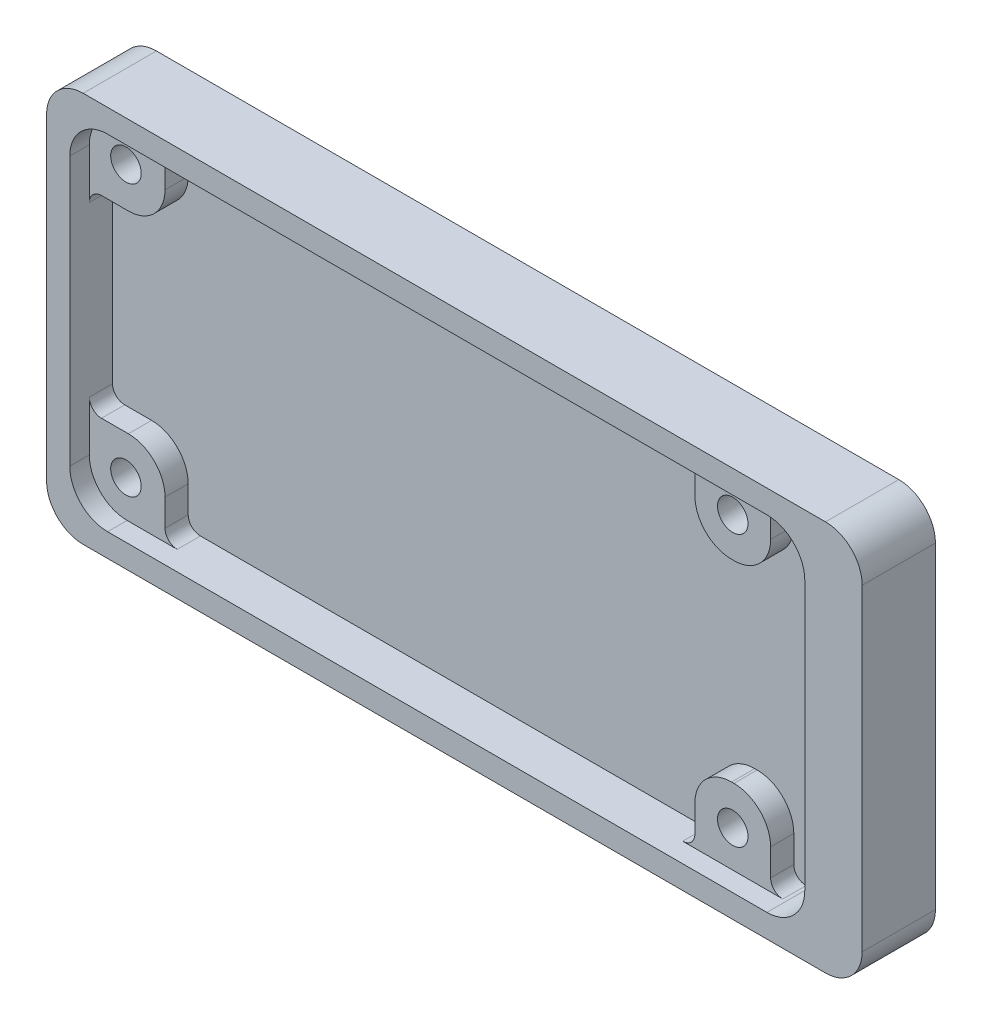
SolidWorks part; units mm, degrees
ref_plane "Спереди" through (0, 0, 0) normal (0, 0, 1) x (1, 0, 0)
ref_plane "Сверху" through (0, 0, 0) normal (0, 1, 0) x (1, 0, 0)
ref_plane "Справа" through (0, 0, 0) normal (1, 0, 0) x (0, 0, -1)
sketch "Эскиз1" plane through (0, 0, 0) normal (0, 0, 1) x (1, 0, 0)
  line L1 (3, 0) -> (63.8, 0)
  line L2 (0, 3) -> (0, 29)
  line L3 (3, 32) -> (63.8, 32)
  line L4 (66.8, 3) -> (66.8, 29)
  arc A0 (63.8, 0) -> (66.8, 3) centre (63.8, 3) ccw
  arc A1 (63.8, 32) -> (66.8, 29) centre (63.8, 29) cw
  arc A2 (3, 0) -> (0, 3) centre (3, 3) cw
  arc A3 (0, 29) -> (3, 32) centre (3, 29) cw
  point P9 (66.8, 32)
  point P12 (0, 0)
  point P15 (0, 32)
  dimension "D3" = 3
  dimension "D1" = 66.8
  dimension "D2" = 32
extrude "Бобышка-Вытянуть1" add sketch "Эскиз1" along normal blind 6
sketch "Эскиз2" plane through (0, 0, 6) normal (0, 0, 1) x (1, 0, 0)
  line L0 (0, 29) -> (0, 3) construction
  line L1 (5, 30.1) -> (59, 30.1)
  line L2 (1.9, 27) -> (1.9, 5)
  line L3 (5, 1.9) -> (59, 1.9)
  line L4 (62.1, 27) -> (62.1, 5)
  line L6 (63.8, 32) -> (3, 32) construction
  arc A0 (59, 30.1) -> (62.1, 27) centre (59, 27) cw
  arc A1 (59, 1.9) -> (62.1, 5) centre (59, 5) ccw
  arc A2 (1.9, 5) -> (5, 1.9) centre (5, 5) ccw
  arc A3 (5, 30.1) -> (1.9, 27) centre (5, 27) ccw
  point P10 (62.1, 30.1)
  point P15 (1.9, 1.9)
  point P18 (1.9, 30.1)
  dimension "D5" = 3.1
  dimension "D1" = 60.2
  dimension "D2" = 28.2
  dimension "D3" = 1.9
  dimension "D4" = 1.9
extrude "Вырез-Вытянуть1" cut sketch "Эскиз2" against normal blind 3.5
sketch "Эскиз3" plane through (0, 0, 2.5) normal (0, 0, 1) x (1, 0, 0)
  line L0 (59, 30.1) -> (5, 30.1) construction
  line L1 (4.9, 30.1) -> (8.1, 30.1)
  line L2 (1.9, 27.1) -> (1.9, 23.9)
  line L3 (1.9, 23.9) -> (5.1, 23.9)
  line L4 (8.1, 30.1) -> (8.1, 26.9)
  line L13 (1.9, 8.1) -> (5.1, 8.1)
  line L14 (1.9, 8.1) -> (1.9, 4.9)
  line L15 (4.9, 1.9) -> (8.1, 1.9)
  line L16 (8.1, 5.1) -> (8.1, 1.9)
  line L17 (1.9, 27) -> (1.9, 5) construction
  line L18 (5, 1.9) -> (59, 1.9) construction
  line L22 (59, 30.1) -> (5, 30.1) construction
  line L23 (51.5, 30.1) -> (57.7, 30.1)
  line L24 (51.5, 30.1) -> (51.5, 26.9)
  line L25 (54.5, 23.9) -> (54.7, 23.9)
  line L26 (57.7, 30.1) -> (57.7, 26.9)
  line L27 (5, 1.9) -> (59, 1.9) construction
  line L28 (51.5, 1.9) -> (57.7, 1.9)
  line L29 (51.5, 1.9) -> (51.5, 5.1)
  line L30 (54.5, 8.1) -> (54.7, 8.1)
  line L31 (57.7, 1.9) -> (57.7, 5.1)
  line L32 (62.1, 5) -> (62.1, 27) construction
  line L33 (62.1, 5) -> (62.1, 27) construction
  arc A2 (5.1, 8.1) -> (8.1, 5.1) centre (5.1, 5.1) cw
  arc A3 (1.9, 4.9) -> (4.9, 1.9) centre (4.9, 4.9) ccw
  arc A4 (5.1, 23.9) -> (8.1, 26.9) centre (5.1, 26.9) ccw
  arc A5 (4.9, 30.1) -> (1.9, 27.1) centre (4.9, 27.1) ccw
  arc A8 (54.7, 8.1) -> (57.7, 5.1) centre (54.7, 5.1) cw
  arc A9 (51.5, 5.1) -> (54.5, 8.1) centre (54.5, 5.1) cw
  arc A10 (54.7, 23.9) -> (57.7, 26.9) centre (54.7, 26.9) ccw
  arc A11 (51.5, 26.9) -> (54.5, 23.9) centre (54.5, 26.9) ccw
  point P33 (8.1, 8.1)
  point P38 (8.1, 23.9)
  point P42 (57.7, 8.1)
  point P45 (51.5, 8.1)
  point P48 (57.7, 23.9)
  point P51 (51.5, 23.9)
  dimension "D15" = 3
  dimension "D1" = 6.2
  dimension "D2" = 6.2
  dimension "D3" = 0
  dimension "D4" = 0
  dimension "D5" = 6.2
  dimension "D6" = 6.2
  dimension "D7" = 0
  dimension "D8" = 0
  dimension "D9" = 6.2
  dimension "D10" = 6.2
  dimension "D11" = 4.4
  dimension "D12" = 6.2
  dimension "D13" = 6.2
  dimension "D14" = 4.4
extrude "Бобышка-Вытянуть2" add sketch "Эскиз3" along normal blind 1.9
sketch "Эскиз4" plane through (0, 0, 0) normal (0, 0, -1) x (-1, 0, 0)
  line L0 (-63.8, 32) -> (-3, 32) construction
  line L1 (-66.8, 3) -> (-66.8, 29) construction
  line L2 (-3, 0) -> (-63.8, 0) construction
  line L3 (0, 29) -> (0, 3) construction
  circle A0 centre (-54.6, 27.1) radius 1.25
  circle A1 centre (-4.9, 27.1) radius 1.25
  circle A2 centre (-4.9, 4.9) radius 1.25
  circle A3 centre (-54.6, 4.9) radius 1.25
  dimension "D1" = 4.9
  dimension "D9" = 2.5
  dimension "D10" = 2.5
  dimension "D11" = 2.5
  dimension "D12" = 2.5
  dimension "D2" = 12.2
  dimension "D3" = 4.9
  dimension "D4" = 12.2
  dimension "D5" = 4.9
  dimension "D6" = 4.9
  dimension "D7" = 4.9
  dimension "D8" = 4.9
extrude "Вырез-Вытянуть2" cut sketch "Эскиз4" against normal through all
sketch "Эскиз11" plane through (0, 0, 0) normal (0, 0, -1) x (-1, 0, 0)
  circle A0 centre (-54.6, 27.1) radius 2.4
  circle A1 centre (-4.9, 27.1) radius 2.4
  circle A2 centre (-54.6, 4.9) radius 2.4
  circle A3 centre (-4.9, 4.9) radius 2.4
  dimension "D1" = 4.8
  dimension "D2" = 4.8
  dimension "D3" = 4.8
  dimension "D4" = 4.8
extrude "Вырез-Вытянуть3" cut sketch "Эскиз11" against normal blind 2.5
fillet "Скругление1" radius 1 8 edges at (51.5, 1.9, 3.45) (57.7, 1.9, 3.45) (1.9, 8.1, 3.45) (8.1, 1.9, 3.45) (1.9, 23.9, 3.45) (8.1, 30.1, 3.45) (57.7, 30.1, 3.45) (51.5, 30.1, 3.45)
